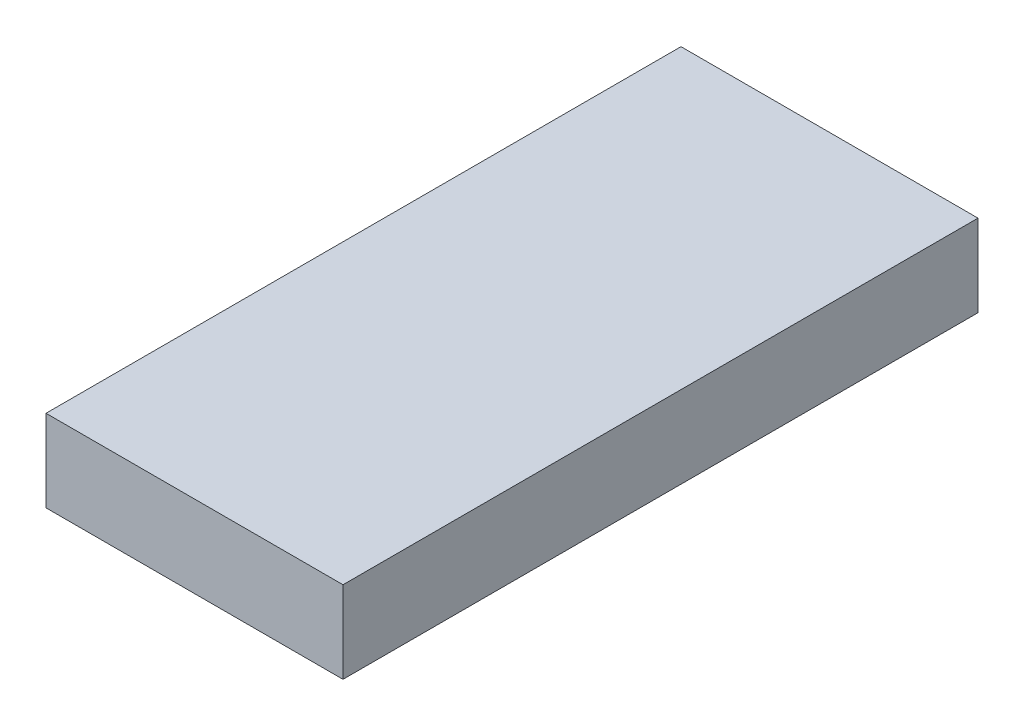
SolidWorks part; units mm, degrees
ref_plane "Front" through (0, 0, 0) normal (0, 0, 1) x (1, 0, 0)
ref_plane "Top" through (0, 0, 0) normal (0, 1, 0) x (1, 0, 0)
ref_plane "Right" through (0, 0, 0) normal (1, 0, 0) x (0, 0, -1)
sketch "Sketch1" plane through (0, 0, 0) normal (0, 1, 0) x (1, 0, 0)
  line L1 (0, 0) -> (73.66, 0)
  line L2 (0, 0) -> (0, 157.48)
  line L3 (0, 157.48) -> (73.66, 157.48)
  line L4 (73.66, 0) -> (73.66, 157.48)
  dimension "D1" = 157.48
  dimension "D2" = 73.66
extrude "Boss-Extrude1" add sketch "Sketch1" along normal blind 20.32
